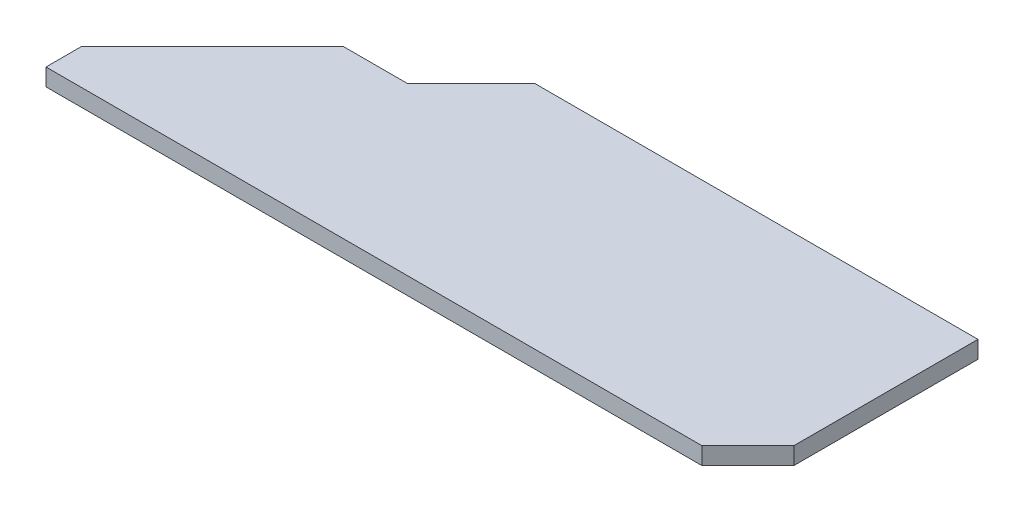
SolidWorks part; units mm, degrees
ref_plane "Front Plane" through (0, 0, 0) normal (0, 0, 1) x (1, 0, 0)
ref_plane "Top Plane" through (0, 0, 0) normal (0, 1, 0) x (1, 0, 0)
ref_plane "Right Plane" through (0, 0, 0) normal (1, 0, 0) x (0, 0, -1)
sketch "Sketch1" plane through (0, 0, 0) normal (0, 1, 0) x (1, 0, 0)
  line L1 (-81.4855, 32.7355) -> (32.5145, 32.7355)
  line L2 (-81.4855, 32.7355) -> (-81.4855, -7.2645)
  line L3 (-81.4855, -7.2645) -> (32.5145, -7.2645)
  line L4 (32.5145, 32.7355) -> (32.5145, -7.2645)
  dimension "D1" = 40
  dimension "D2" = 114
extrude "Boss-Extrude1" add sketch "Sketch1" along normal blind 3
sketch "Sketch2" plane through (0, 3, 0) normal (0, 1, 0) x (1, 0, 0)
  line L0 (-36.4855, 32.7355) -> (-44.1659, 25.0551)
  line L1 (32.5145, 32.7355) -> (-81.4855, 32.7355) construction
  line L3 (-72.5323, 7.8752) -> (-81.4855, -1.0779)
  line L4 (-81.4855, 32.7355) -> (-81.4855, -7.2645) construction
  line L5 (-81.4855, -1.0779) -> (-81.4855, 32.7355)
  line L6 (-81.4855, 32.7355) -> (-36.4855, 32.7355)
  line L10 (-44.1659, 25.0551) -> (-47.5608, 21.6602)
  line L11 (-47.5608, 21.6602) -> (-58.7474, 21.6602)
  line L12 (-72.5323, 7.8752) -> (-58.7474, 21.6602)
  dimension "D1" = 45
  dimension "D2" = 45
extrude "Cut-Extrude1" cut sketch "Sketch2" against normal through all
sketch "Sketch3" plane through (0, 3, 0) normal (0, 1, 0) x (1, 0, 0)
  line L0 (32.5145, -7.2645) -> (40.5145, 0.7355)
  line L1 (40.5145, 0.7355) -> (40.5145, 32.7355)
  line L2 (40.5145, 32.7355) -> (32.5145, 32.7355)
  line L3 (32.5145, 32.7355) -> (32.5145, -7.2645)
  line L4 (32.5145, -7.2645) -> (52.4468, -16.6269)
  dimension "D1" = 45
  dimension "D2" = 8
extrude "Boss-Extrude2" add sketch "Sketch3" against normal through all contours L0 L1 L2 L3
